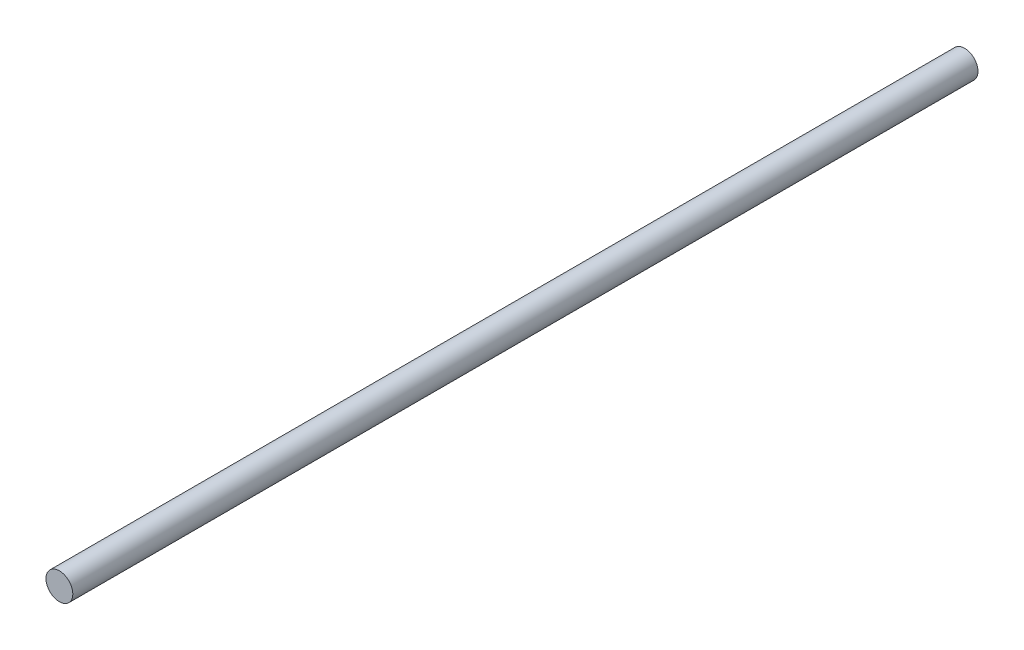
SolidWorks part; units mm, degrees
ref_plane "Plan de face" through (0, 0, 0) normal (0, 0, 1) x (1, 0, 0)
ref_plane "Plan de dessus" through (0, 0, 0) normal (0, 1, 0) x (1, 0, 0)
ref_plane "Plan de droite" through (0, 0, 0) normal (1, 0, 0) x (0, 0, -1)
sketch "Esquisse1" plane through (0, 0, 0) normal (0, 0, 1) x (1, 0, 0)
  circle A0 centre (0, 0) radius 4
  dimension "D1" = 8
extrude "Boss.-Extru.1" add sketch "Esquisse1" along normal blind 270
